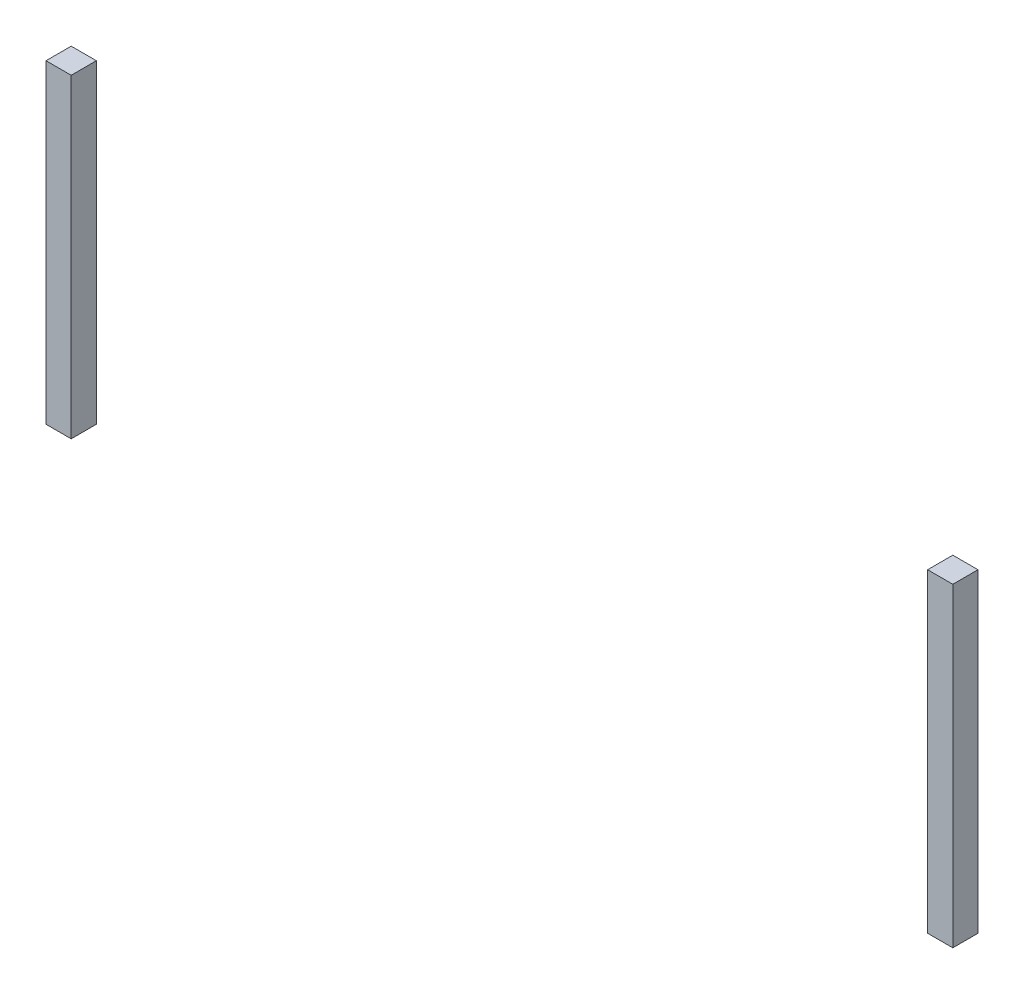
SolidWorks part; units mm, degrees
ref_plane "Front Plane" through (0, 0, 0) normal (0, 0, 1) x (1, 0, 0)
ref_plane "Top Plane" through (0, 0, 0) normal (0, 1, 0) x (1, 0, 0)
ref_plane "Right Plane" through (0, 0, 0) normal (1, 0, 0) x (0, 0, -1)
sketch "Sketch1" plane through (0, 0, 0) normal (0, 1, 0) x (1, 0, 0)
  line L1 (-1.7, 0) -> (-1.8, 0)
  line L2 (-1.7, 0) -> (-1.7, 0.1)
  line L3 (-1.7, 0.1) -> (-1.8, 0.1)
  line L4 (-1.8, 0) -> (-1.8, 0.1)
  line L5 (1.7, 0) -> (1.8, 0)
  line L6 (1.7, 0) -> (1.7, 0.1)
  line L7 (1.7, 0.1) -> (1.8, 0.1)
  line L8 (1.8, 0) -> (1.8, 0.1)
  point P8 (-1.75, 0)
  point P10 (1.75, 0)
  dimension "D1" = 0.1
  dimension "D2" = 0.1
  dimension "D3" = 1.75
  dimension "D4" = 1.75
extrude "Boss-Extrude1" add sketch "Sketch1" along normal blind 1.25
